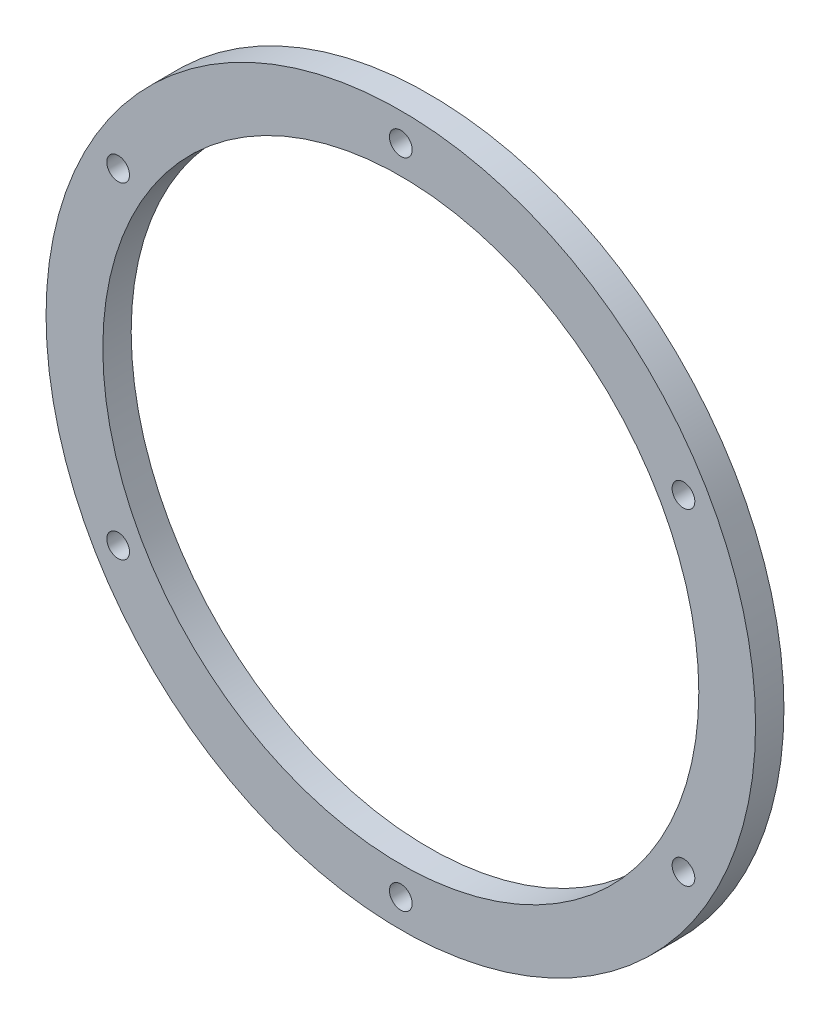
SolidWorks part; units mm, degrees
material "Brass"
ref_plane "Front Plane" through (0, 0, 0) normal (0, 0, 1) x (1, 0, 0)
ref_plane "Top Plane" through (0, 0, 0) normal (0, 1, 0) x (1, 0, 0)
ref_plane "Right Plane" through (0, 0, 0) normal (1, 0, 0) x (0, 0, -1)
sketch "Sketch1" plane through (0, 0, 0) normal (0, 0, 1) x (1, 0, 0)
  circle A0 centre (0, 0) radius 105
  circle A1 centre (0, 0) radius 125
  dimension "D1" = 210
  dimension "D2" = 250
extrude "Body" add sketch "Sketch1" along normal mid plane 10
sketch "Sketch2" plane through (0, 0, 5) normal (0, 0, 1) x (1, 0, 0)
  line L0 (0, -71.4075) -> (0, 70.4111) construction
  circle A0 centre (0, 115) radius 4
  circle A1 centre (0, 0) radius 115 construction
  dimension "D1" = 8
  dimension "D2" = 230
extrude "Cut-Extrude1" cut sketch "Sketch2" against normal through all
pattern_circular "Holes" count 6 over 360 about axis through (0, 0, 0) along (0, 0, 1) of "Cut-Extrude1"
